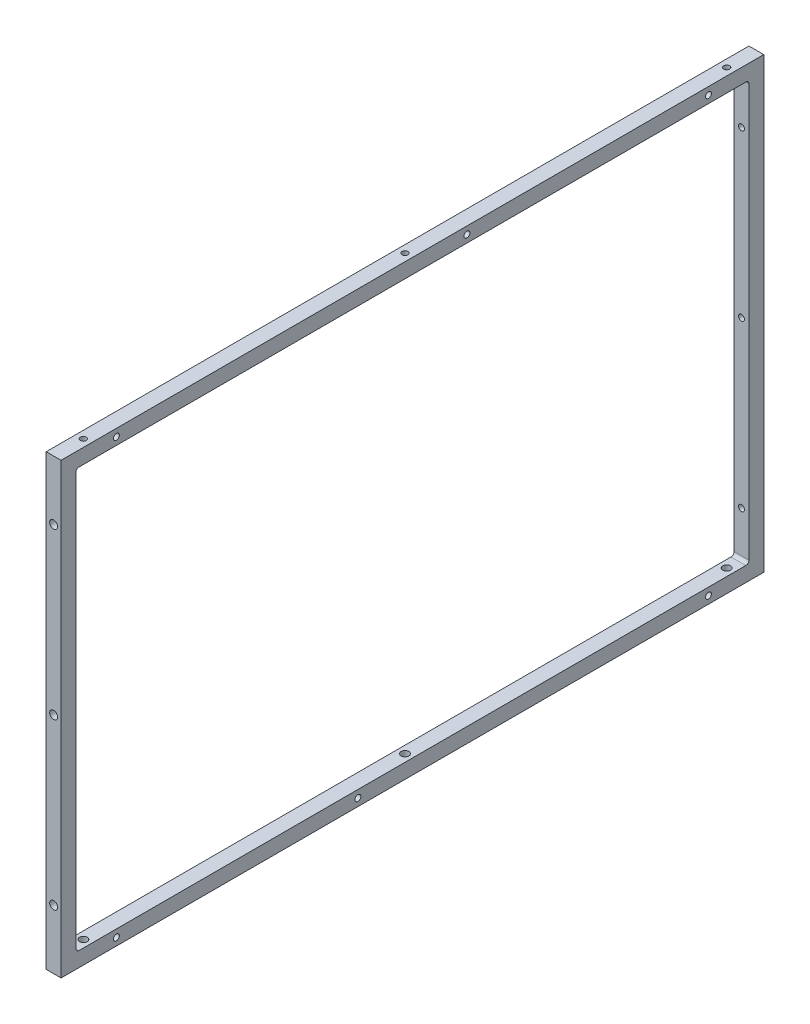
SolidWorks part; units mm, degrees
material "6061-T6 (SS)"
ref_plane "Front Plane" through (0, 0, 0) normal (0, 0, 1) x (1, 0, 0)
ref_plane "Top Plane" through (0, 0, 0) normal (0, 1, 0) x (1, 0, 0)
ref_plane "Right Plane" through (0, 0, 0) normal (1, 0, 0) x (0, 0, -1)
sketch "Sketch1" plane through (0, 0, 0) normal (1, 0, 0) x (0, 0, -1)
  line L0 (225.5, 143.8857) -> (-225.5, -143.8857) construction
  line L1 (-225.5, 143.8857) -> (225.5, 143.8857)
  line L2 (-225.5, 143.8857) -> (-225.5, -143.8857)
  line L3 (-225.5, -143.8857) -> (225.5, -143.8857)
  line L4 (225.5, 143.8857) -> (225.5, -143.8857)
  point P4 (0, 0)
  dimension "D1" = 451
  dimension "D2" = 287.7714
extrude "Extrude-Thin1" add sketch "Sketch1" along normal blind 9.525 thin
fillet "Fillet1" radius 2 4 edges at (4.7625, 134.3607, 215.975) (4.7625, -134.3607, 215.975) (4.7625, -134.3607, -215.975) (4.7625, 134.3607, -215.975)
hole_wizard "#10 Clearance Hole1" positions "Sketch4" profile "Sketch3" hole size "#10" standard "ANSI Inch" end condition up to next
sketch "Sketch4" plane through (0, -143.8857, 0) normal (0, -1, 0) x (-1, 0, 0)
  line L0 (-4.7625, 225.5) -> (-4.7625, 470.0554) construction
  line L1 (-9.525, 225.5) -> (0, 225.5) construction
  line L2 (0, 0) -> (172.0278, 0) construction
  line L3 (0, -225.5) -> (0, 225.5) construction
  point P0 (-4.7625, 206.45)
  point P14 (-4.7625, 0)
  point P19 (-4.7625, -206.45)
  dimension "D1" = 19.05
sketch "Sketch3" plane through (4.7625, -143.8857, -206.45) normal (1, 0, 0) x (0, 0, -1)
  line L0 (0, 0) -> (0, 9.525)
  line L1 (0, 9.525) -> (2.4892, 9.525)
  line L2 (2.4892, 9.525) -> (2.4892, 0)
  line L5 (2.4892, 0) -> (0, 0)
  line L11 (0, -6.35) -> (0, 107.95) construction
  dimension "Thru Hole Dia." = 4.9784
  dimension "Thru Hole Depth" = 9.525
hole_wizard "#10-24 Tapped Hole1" positions "Sketch6" profile "Sketch5" tap size "#10-24" standard "ANSI Inch"
sketch "Sketch6" plane through (0, 0, -225.5) normal (0, 0, -1) x (-1, 0, 0)
  line L0 (-4.7625, 143.8857) -> (-4.7625, 277.6735) construction
  line L1 (-9.525, 143.8857) -> (0, 143.8857) construction
  line L2 (0, 0) -> (108.9578, 0) construction
  line L3 (0, -143.8857) -> (0, 143.8857) construction
  point P0 (-4.7625, 105.7857)
  point P14 (0, 0)
  point P15 (-4.7625, 0)
  point P18 (-4.7625, -105.7857)
  dimension "D1" = 38.1
sketch "Sketch5" plane through (4.7625, 105.7857, -225.5) normal (1, 0, 0) x (0, 1, 0)
  line L0 (0, 0) -> (0, 16.0908)
  line L1 (0, 16.0908) -> (1.8986, 14.95)
  line L2 (1.8986, 14.95) -> (1.8986, 0)
  line L5 (1.8986, 0) -> (0, 0)
  line L10 (0, 16.0908) -> (-1.8986, 14.95) construction
  line L11 (0, -6.35) -> (0, 107.95) construction
  dimension "Tap Drill Dia." = 3.7973
  dimension "Tap Drill Depth" = 14.95
  dimension "Drill Angle" = 118
cosmetic thread "Hole Thread1" parameters "D1"=9.525, "D2"=4.826
cosmetic thread "Hole Thread2" parameters "D1"=9.525, "D2"=4.826
cosmetic thread "Hole Thread3" parameters "D1"=9.525, "D2"=4.826
hole_wizard "#10 Clearance Hole2" positions "Sketch8" profile "Sketch7" hole size "#10" standard "ANSI Inch"
sketch "Sketch8" plane through (0, 0, 225.5) normal (0, 0, 1) x (1, 0, 0)
  point P0 (4.7625, 105.7857)
  point P3 (4.7625, 0)
  point P6 (4.7625, -105.7857)
sketch "Sketch7" plane through (4.7625, 105.7857, 225.5) normal (1, 0, 0) x (0, -1, 0)
  line L0 (0, 0) -> (0, 21.5338)
  line L1 (0, 21.5338) -> (2.5527, 20)
  line L2 (2.5527, 20) -> (2.5527, 0)
  line L5 (2.5527, 0) -> (0, 0)
  line L10 (0, 21.5338) -> (-2.5527, 20) construction
  line L11 (0, -6.35) -> (0, 107.95) construction
  dimension "Hole Dia." = 5.1054
  dimension "Hole Depth" = 20
  dimension "Drill Angle" = 118
hole_wizard "#10-24 Tapped Hole2 side" positions "Sketch10" profile "Sketch9" tap size "#10-24" standard "ANSI Inch" end condition through all
sketch "Sketch10" plane through (0, 0, 0) normal (-1, 0, 0) x (0, 0, 1)
  line L0 (0, 0) -> (-63.9305, 0) construction
  line L1 (0, 0) -> (0, 94.9596) construction
  line L2 (-213.975, 134.3607) -> (213.975, 134.3607) construction
  line L3 (-225.5, 143.8857) -> (225.5, 143.8857) construction
  line L4 (-171.0494, 139.1232) -> (-144.3476, 139.1232) construction
  line L5 (-171.0494, -139.1232) -> (-144.3476, -139.1232) construction
  circle A0 centre (-190, 139.1232) radius 4.7625 construction
  point P0 (-190, 139.1232)
  point P19 (-35, 139.1232)
  point P22 (-190, -139.1232)
  point P23 (35, -139.1232)
  point P26 (190, -139.1232)
  point P27 (190, 139.1232)
  dimension "D1" = 190
  dimension "D2" = 35
  dimension "D3" = 35
sketch "Sketch9" plane through (0, 139.1232, -190) normal (0, 1, 0) x (0, 0, 1)
  line L0 (0, 0) -> (0, 9.525)
  line L1 (0, 9.525) -> (1.8986, 9.525)
  line L2 (1.8986, 9.525) -> (1.8986, 0)
  line L5 (1.8986, 0) -> (0, 0)
  line L11 (0, -6.35) -> (0, 107.95) construction
  dimension "Thru Tap Drill Dia." = 3.7973
  dimension "Thru Tap Drill Depth" = 9.525
cosmetic thread "Hole Thread5" parameters "D1"=9.525, "D2"=4.826
cosmetic thread "Hole Thread6" parameters "D1"=9.525, "D2"=4.826
cosmetic thread "Hole Thread7" parameters "D1"=9.525, "D2"=4.826
cosmetic thread "Hole Thread8" parameters "D1"=9.525, "D2"=4.826
cosmetic thread "Hole Thread9" parameters "D1"=9.525, "D2"=4.826
cosmetic thread "Hole Thread10" parameters "D1"=9.525, "D2"=4.826
hole_wizard "#10-24 Tapped Hole2" positions "Sketch13" profile "Sketch12" tap size "#10-24" standard "ANSI Inch"
sketch "Sketch13" plane through (0, 143.8857, 0) normal (0, 1, 0) x (1, 0, 0)
  point P0 (4.7625, 206.45)
  point P3 (4.7625, 0)
  point P6 (4.7625, -206.45)
sketch "Sketch12" plane through (4.7625, 143.8857, -206.45) normal (1, 0, 0) x (0, 0, 1)
  line L0 (0, 0) -> (0, 16.0908)
  line L1 (0, 16.0908) -> (1.8986, 14.95)
  line L2 (1.8986, 14.95) -> (1.8986, 0)
  line L5 (1.8986, 0) -> (0, 0)
  line L10 (0, 16.0908) -> (-1.8986, 14.95) construction
  line L11 (0, -6.35) -> (0, 107.95) construction
  dimension "Tap Drill Dia." = 3.7973
  dimension "Tap Drill Depth" = 14.95
  dimension "Drill Angle" = 118
cosmetic thread "Hole Thread11" parameters "D1"=9.525, "D2"=4.826
cosmetic thread "Hole Thread12" parameters "D1"=9.525, "D2"=4.826
cosmetic thread "Hole Thread13" parameters "D1"=9.525, "D2"=4.826
